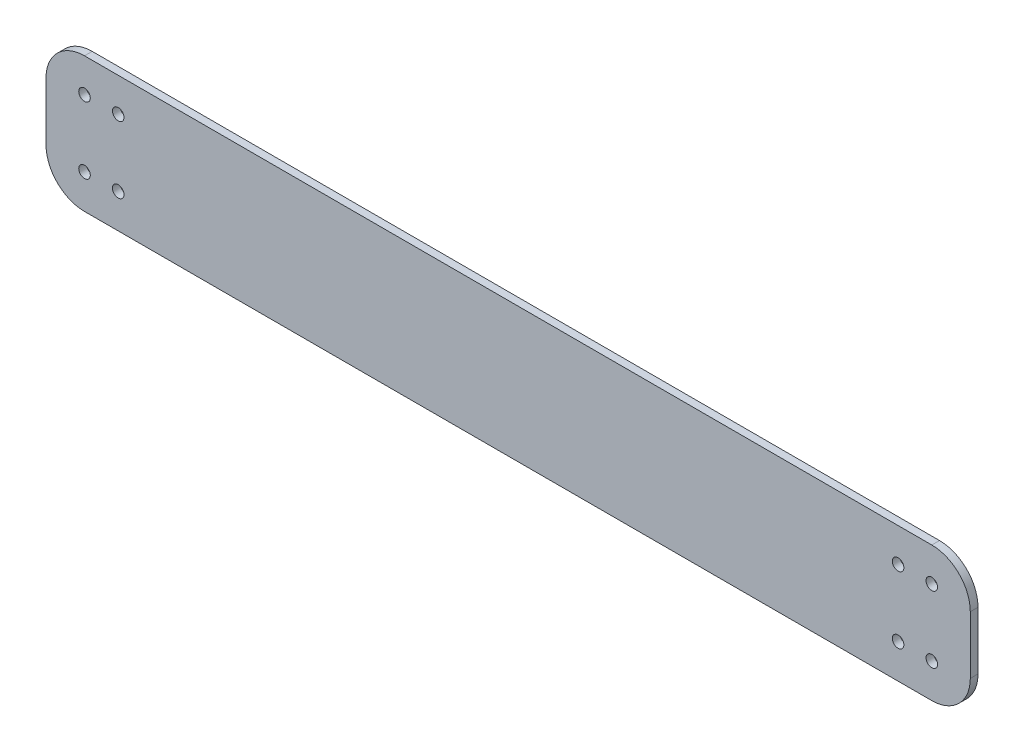
SolidWorks part; units mm, degrees
ref_plane "前视基准面" through (0, 0, 0) normal (0, 0, 1) x (1, 0, 0)
ref_plane "上视基准面" through (0, 0, 0) normal (0, 1, 0) x (1, 0, 0)
ref_plane "右视基准面" through (0, 0, 0) normal (1, 0, 0) x (0, 0, -1)
other "Configuration Table"
sketch "草图2" plane through (0, 0, 0) normal (0, 0, 1) x (1, 0, 0)
  line L0 (-50.3604, 22.3704) -> (169.6396, 22.3704)
  line L1 (179.6396, 12.3704) -> (179.6396, -2.6296)
  line L2 (169.6396, -12.6296) -> (-50.3604, -12.6296)
  line L3 (-60.3604, -2.6296) -> (-60.3604, 12.3704)
  arc A0 (179.6396, -2.6296) -> (169.6396, -12.6296) centre (169.6396, -2.6296) cw
  arc A1 (169.6396, 22.3704) -> (179.6396, 12.3704) centre (169.6396, 12.3704) cw
  arc A2 (-50.3604, -12.6296) -> (-60.3604, -2.6296) centre (-50.3604, -2.6296) cw
  arc A3 (-50.3604, 22.3704) -> (-60.3604, 12.3704) centre (-50.3604, 12.3704) ccw
  dimension "D1" = 10
  dimension "D2" = 220
  dimension "D3" = 15
extrude "凸台-拉伸1" add sketch "草图2" along normal blind 2
sketch "草图3" plane through (0, 0, 0) normal (0, 0, -1) x (-1, 0, 0)
  line L1 (-59.6396, 22.3704) -> (-59.6396, -12.6296)
  line L3 (-169.6396, 22.3704) -> (50.3604, 22.3704) construction
  line L9 (50.3604, -12.6296) -> (-169.6396, -12.6296) construction
  point P0 (50.3604, 13.6204)
  point P1 (50.3604, -3.7322)
  point P4 (41.6104, 13.6204)
  point P8 (41.6104, -3.7322)
  point P12 (-160.8896, -3.7322)
  point P13 (-169.6396, -3.7322)
  point P15 (-169.6396, 13.6204)
  point P16 (-160.8896, 13.6204)
  dimension "D1" = 8.75
  dimension "D2" = 17.3526
hole_wizard "大小mm 暗销孔2" positions "3D草图4" profile "草图7" hole size "Ø3.0" standard "GB" end condition through all
sketch3d "3D草图4"
  point P0 (-41.6104, 13.6204, 0)
  point P3 (-50.3604, 13.6204, 0)
  point P6 (-41.6104, -3.7322, 0)
  point P9 (-50.3604, -3.7322, 0)
sketch "草图7" plane through (-41.6104, 13.6204, 0) normal (1, 0, 0) x (0, 1, 0)
  line L0 (0, 0) -> (0, 2)
  line L1 (0, 2) -> (1.5, 2)
  line L2 (1.5, 2) -> (1.5, 0)
  line L5 (1.5, 0) -> (0, 0)
  line L11 (0, -6.35) -> (0, 107.95) construction
  dimension "通孔孔直径" = 3
  dimension "通孔孔深度" = 2
sketch3d "3D草图5" plane through (0, 0, 0) normal (0, 0, 1) x (1, 0, 0)
hole_wizard "大小mm 暗销孔3" positions "3D草图6" profile "草图8" hole size "Ø3.0" standard "GB" end condition through all
sketch3d "3D草图6"
  point P0 (169.6396, 13.6204, 0)
  point P3 (160.8896, 13.6204, 0)
  point P6 (160.8896, -3.7322, 0)
  point P9 (169.6396, -3.7322, 0)
sketch "草图8" plane through (169.6396, 13.6204, 0) normal (1, 0, 0) x (0, 1, 0)
  line L0 (0, 0) -> (0, 2)
  line L1 (0, 2) -> (1.5, 2)
  line L2 (1.5, 2) -> (1.5, 0)
  line L5 (1.5, 0) -> (0, 0)
  line L11 (0, -6.35) -> (0, 107.95) construction
  dimension "通孔孔直径" = 3
  dimension "通孔孔深度" = 2
